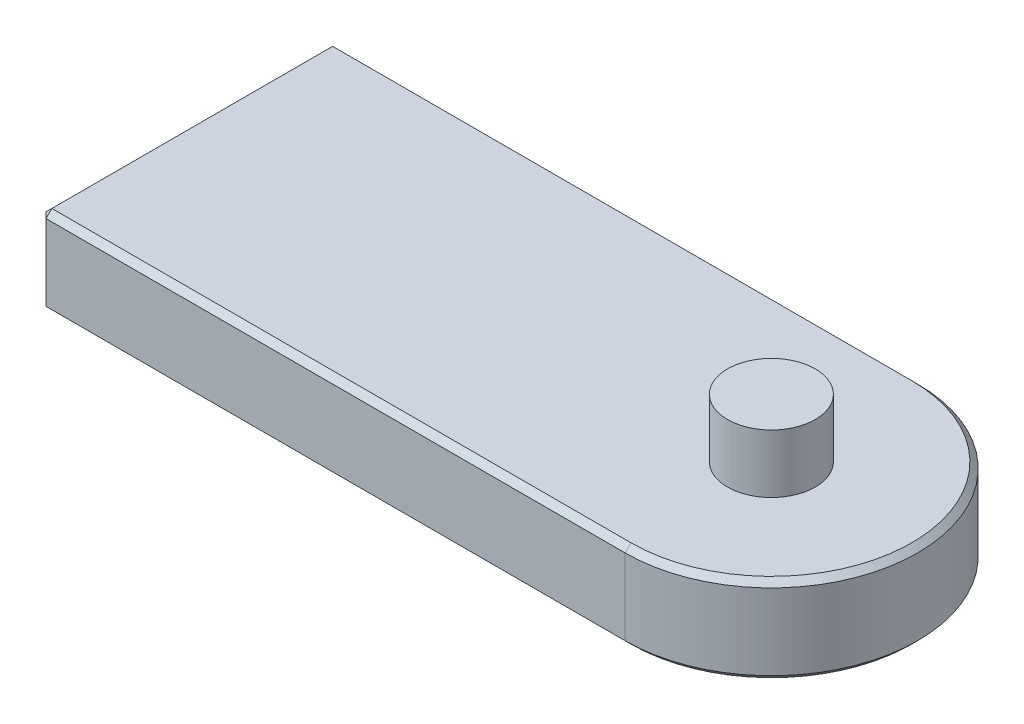
SolidWorks part; units mm, degrees
ref_plane "Front Plane" through (0, 0, 0) normal (0, 0, 1) x (1, 0, 0)
ref_plane "Top Plane" through (0, 0, 0) normal (0, 1, 0) x (1, 0, 0)
ref_plane "Right Plane" through (0, 0, 0) normal (1, 0, 0) x (0, 0, -1)
sketch "Sketch1" plane through (0, 0, 0) normal (0, 1, 0) x (1, 0, 0)
  line L0 (100, 50) -> (-100, 50)
  line L1 (-100, 50) -> (-100, -50)
  line L2 (-100, -50) -> (100, -50)
  arc A0 (100, -50) -> (100, 50) centre (100, 0) ccw
  dimension "D1" = 100
  dimension "D2" = 100
  dimension "D3" = 200
extrude "Boss-Extrude1" add sketch "Sketch1" along normal blind 30
sketch "Sketch2" plane through (0, 30, 0) normal (0, 1, 0) x (1, 0, 0)
  circle A0 centre (100, 0) radius 15
  dimension "D1" = 30
extrude "Boss-Extrude2" add sketch "Sketch2" along normal blind 20
chamfer "Chamfer1" distance 2 angle 45 10 edges at (0, 0, 50) (0, 0, -50) (150, 0, 0) (-100, 15, -50) (-100, 0, 0) (-100, 15, 50) (-100, 30, 0) (0, 30, -50) (150, 30, 0) (0, 30, 50)
